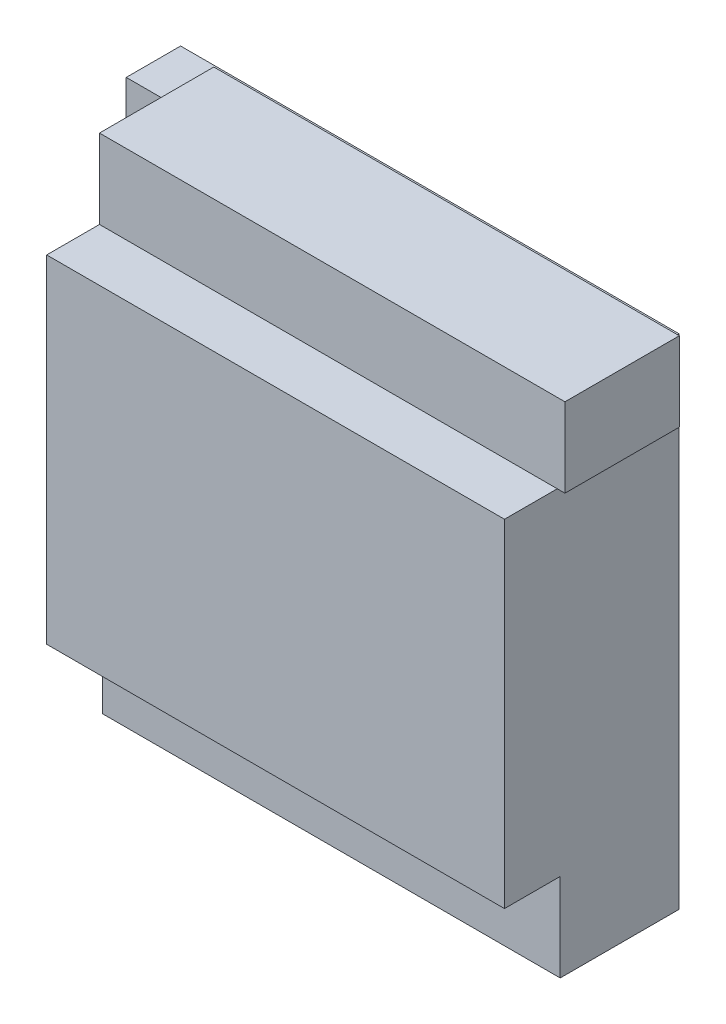
SolidWorks part; units mm, degrees
ref_plane "Front Plane" through (0, 0, 0) normal (0, 0, 1) x (1, 0, 0)
ref_plane "Top Plane" through (0, 0, 0) normal (0, 1, 0) x (1, 0, 0)
ref_plane "Right Plane" through (0, 0, 0) normal (1, 0, 0) x (0, 0, -1)
sketch "Sketch1" plane through (0, 0, 0) normal (0, 0, 1) x (1, 0, 0)
  line L0 (-78.65, 85) -> (-78.65, 74.84) construction
  line L1 (-85, -85) -> (85, -85)
  line L2 (-85, -85) -> (-85, 85)
  line L3 (-85, 85) -> (85, 85)
  line L4 (85, -85) -> (85, 85)
  line L5 (-85, -85) -> (85, 85) construction
  line L6 (-85, 85) -> (85, -85) construction
  line L7 (78.83, 85) -> (78.83, 51.98) construction
  line L8 (-78.65, 74.84) -> (78.83, 74.84) construction
  line L9 (-78.65, 74.84) -> (-78.65, -80.1) construction
  line L10 (-78.65, -80.1) -> (78.83, -80.1) construction
  circle A0 centre (-78.65, 74.84) radius 1.98
  circle A1 centre (78.83, 51.98) radius 1.98
  circle A2 centre (-78.65, -80.1) radius 1.98
  circle A3 centre (78.83, -80.1) radius 1.98
  point P0 (0, 0)
  dimension "D5" = 3.96
  dimension "D8" = 3.96
  dimension "D10" = 3.96
  dimension "D11" = 3.96
  dimension "D1" = 170
  dimension "D2" = 170
  dimension "D3" = 6.35
  dimension "D4" = 10.16
  dimension "D6" = 157.48
  dimension "D7" = 22.86
  dimension "D9" = 154.94
extrude "Boss-Extrude1" add sketch "Sketch1" along normal blind 2.54
sketch "Sketch2" plane through (0, 0, 2.54) normal (0, 0, 1) x (1, 0, 0)
  line L1 (-71.13, 60) -> (87.62, 60)
  line L2 (-71.13, 60) -> (-71.13, 87)
  line L3 (-71.13, 87) -> (87.62, 87)
  line L4 (87.62, 60) -> (87.62, 87)
  line L5 (-85, -85) -> (85, -85) construction
  point P4 (-78.65, 74.84)
  dimension "D1" = 158.75
  dimension "D2" = 7.52
  dimension "D3" = 27
  dimension "D4" = 172
extrude "Boss-Extrude2" add sketch "Sketch2" along normal blind 39
sketch "Sketch4" plane through (0, 0, 2.54) normal (0, 0, 1) x (1, 0, 0)
  line L0 (-85, -85) -> (85, -85) construction
  line L1 (-85, 85) -> (-71.13, 85)
  line L2 (-85, 85) -> (-85, -85)
  line L3 (-85, -85) -> (-71.13, -85)
  line L4 (-71.13, 85) -> (-71.13, -85)
extrude "Boss-Extrude3" add sketch "Sketch4" along normal blind 16
sketch "Sketch6" plane through (0, 0, 2.54) normal (0, 0, 1) x (1, 0, 0)
  line L0 (-71.13, -85) -> (-71.13, 60) construction
  line L1 (85, -85) -> (-71.13, -85)
  line L2 (85, -85) -> (85, -55)
  line L3 (85, -55) -> (-71.13, -55)
  line L4 (-71.13, -85) -> (-71.13, -55)
  dimension "D1" = 30
extrude "Boss-Extrude4" add sketch "Sketch6" along normal blind 38
sketch "Sketch5" plane through (0, 0, 2.54) normal (0, 0, 1) x (1, 0, 0)
  line L0 (85, -55) -> (85, 60) construction
  line L1 (-71.13, 60) -> (85, 60)
  line L2 (-71.13, 60) -> (-71.13, -55)
  line L3 (-71.13, -55) -> (85, -55)
  line L4 (85, 60) -> (85, -55)
  line L7 (85, -55) -> (-71.13, -55) construction
extrude "Boss-Extrude5" add sketch "Sketch5" along normal blind 57
